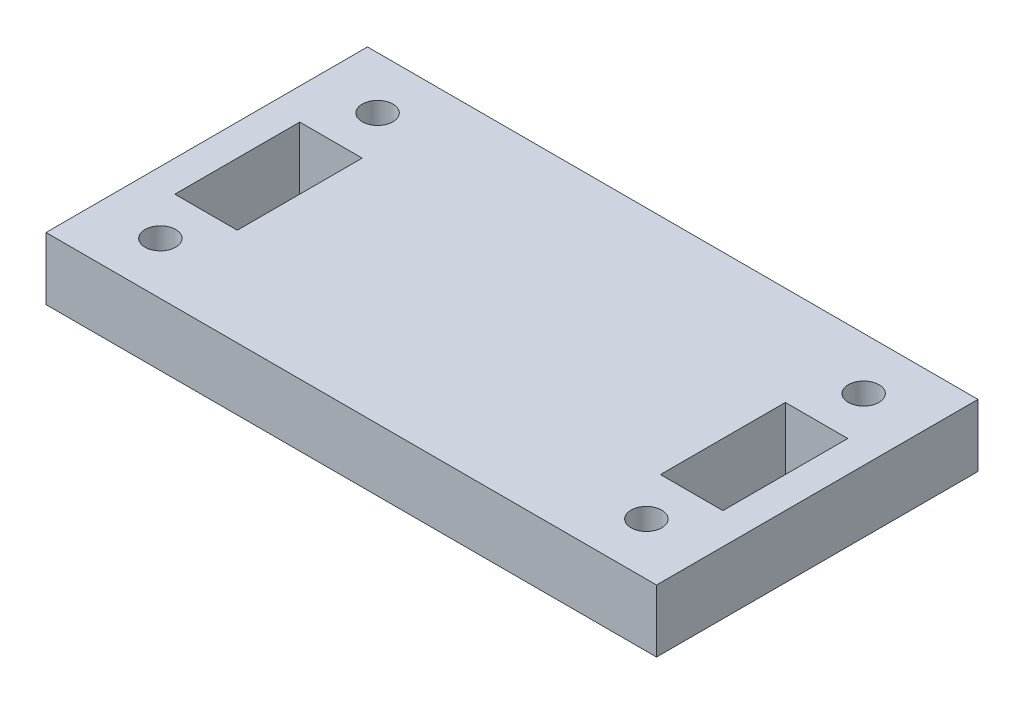
SolidWorks part; units mm, degrees
ref_plane "Front Plane" through (0, 0, 0) normal (0, 0, 1) x (1, 0, 0)
ref_plane "Top Plane" through (0, 0, 0) normal (0, 1, 0) x (1, 0, 0)
ref_plane "Right Plane" through (0, 0, 0) normal (1, 0, 0) x (0, 0, -1)
sketch "Sketch1" plane through (0, 0, 0) normal (0, 1, 0) x (1, 0, 0)
  line L0 (0, 0) -> (9.0486, 0) construction
  line L1 (-29.6847, 16.3436) -> (29.6847, 16.3436)
  line L2 (31.0388, 16.3436) -> (29.6847, 16.3436)
  line L3 (-29.6847, -16.3436) -> (29.6847, -16.3436)
  line L4 (21.5138, 6.2816) -> (27.8638, 6.2816)
  line L5 (-29.6847, 16.3436) -> (29.6847, -16.3436) construction
  line L6 (-29.6847, -16.3436) -> (29.6847, 16.3436) construction
  line L7 (0, 0) -> (0, 11.0441) construction
  line L8 (-21.5138, 6.2816) -> (-27.8638, 6.2816)
  line L9 (-21.5138, 6.2816) -> (-21.5138, -6.4184)
  line L10 (-21.5138, -6.4184) -> (-27.8638, -6.4184)
  line L11 (-27.8638, 6.2816) -> (-27.8638, -6.4184)
  line L12 (-29.6847, -16.3436) -> (-31.0388, -16.3436)
  line L13 (-31.0388, -16.3436) -> (-31.0388, 16.3436)
  line L14 (-31.0388, 16.3436) -> (-29.6847, 16.3436)
  line L15 (31.0388, -16.3436) -> (31.0388, 16.3436)
  line L16 (29.6847, -16.3436) -> (31.0388, -16.3436)
  line L17 (27.8638, 6.2816) -> (27.8638, -6.4184)
  line L18 (21.5138, -6.4184) -> (27.8638, -6.4184)
  line L19 (21.5138, 6.2816) -> (21.5138, -6.4184)
  line L20 (-24.6888, 6.2816) -> (-24.6888, -20.9393) construction
  line L21 (-31.0388, -11.0539) -> (31.0388, -11.0539) construction
  circle A0 centre (-24.7096, 11.0441) radius 1.5621
  circle A1 centre (-24.7096, -11.0441) radius 1.5621
  circle A2 centre (24.7096, 11.0441) radius 1.5621
  circle A3 centre (24.7096, -11.0441) radius 1.5621
  point P0 (0, 0)
  dimension "D3" = 3.1242
  dimension "D1" = 43.0276
  dimension "D2" = 6.35
  dimension "D4" = 3.175
  dimension "D5" = 12.7
extrude "Boss-Extrude1" add sketch "Sketch1" along normal blind 6.35
